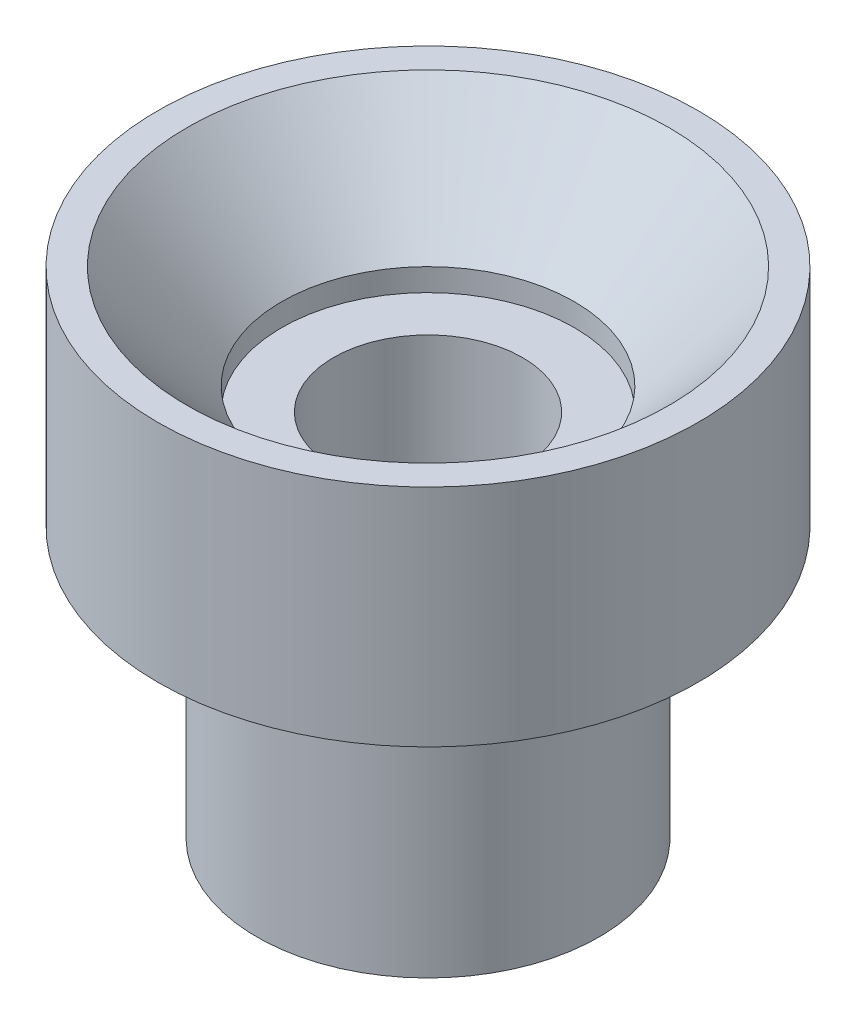
SolidWorks part; units mm, degrees
ref_plane "Front" through (0, 0, 0) normal (0, 0, 1) x (1, 0, 0)
ref_plane "Top" through (0, 0, 0) normal (0, 1, 0) x (1, 0, 0)
ref_plane "Right" through (0, 0, 0) normal (1, 0, 0) x (0, 0, -1)
sketch "Sketch1" plane through (0, 0, 0) normal (0, 0, 1) x (1, 0, 0)
  line L1 (2.1, 0) -> (2.1, 8.2)
  line L3 (5.35, 11) -> (6, 11)
  line L4 (6, 11) -> (6, 6)
  line L5 (6, 6) -> (3.8, 6)
  line L6 (3.8, 6) -> (3.8, 0)
  line L7 (3.8, 0) -> (2.1, 0)
  line L8 (3.25, 8.7) -> (5.35, 11)
  line L9 (0, 0) -> (0, 16.7171) construction
  line L10 (3.25, 8.7) -> (3.25, 8.2)
  line L11 (3.25, 8.2) -> (2.1, 8.2)
  dimension "D1" = 4.2
  dimension "D2" = 7.6
  dimension "D3" = 6
  dimension "D4" = 5
  dimension "D5" = 12
  dimension "D6" = 10.7
  dimension "D7" = 2.3
  dimension "D8" = 0.5
  dimension "D9" = 6.5
revolve "Revolve1" add sketch "Sketch1" angle 360 about L9
